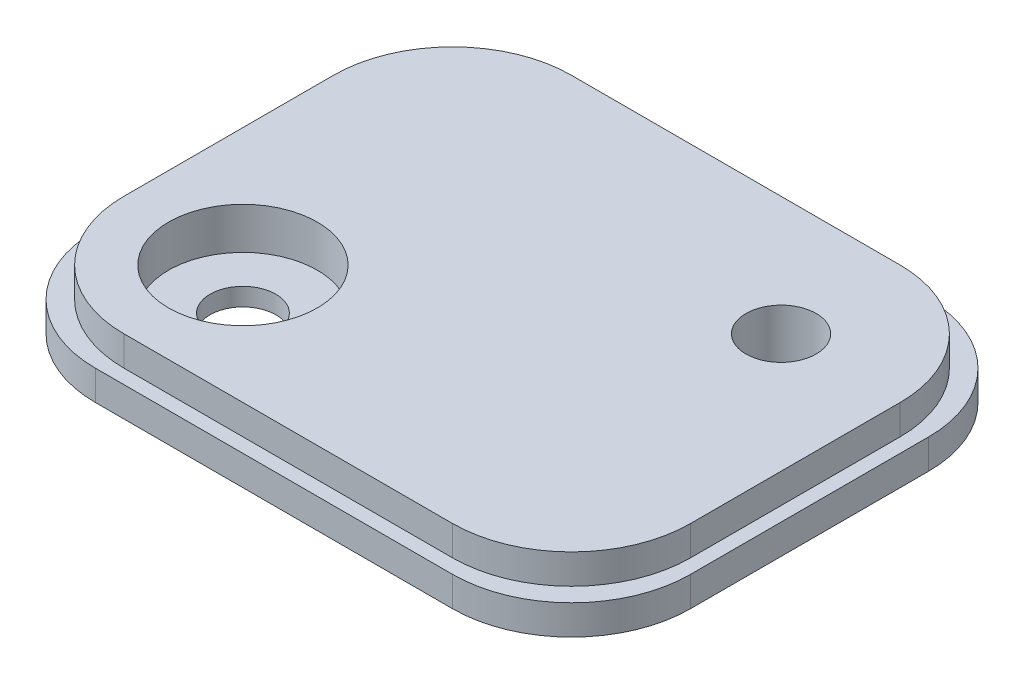
SolidWorks part; units mm, degrees
ref_plane "Front Plane" through (0, 0, 0) normal (0, 0, 1) x (1, 0, 0)
ref_plane "Top Plane" through (0, 0, 0) normal (0, 1, 0) x (1, 0, 0)
ref_plane "Right Plane" through (0, 0, 0) normal (1, 0, 0) x (0, 0, -1)
sketch "Sketch1" plane through (0, 0, 0) normal (0, 1, 0) x (1, 0, 0)
  line L1 (-30, 40) -> (30, 40)
  line L2 (-50, 20) -> (-50, -20)
  line L3 (-30, -40) -> (30, -40)
  line L4 (50, 20) -> (50, -20)
  line L5 (-50, 40) -> (50, -40) construction
  line L6 (-50, -40) -> (50, 40) construction
  arc A0 (30, -40) -> (50, -20) centre (30, -20) ccw
  arc A1 (-30, -40) -> (-50, -20) centre (-30, -20) cw
  arc A2 (30, 40) -> (50, 20) centre (30, 20) cw
  arc A3 (-30, 40) -> (-50, 20) centre (-30, 20) ccw
  point P0 (0, 0)
  dimension "D3" = 20
  dimension "D1" = 100
  dimension "D2" = 80
extrude "Boss-Extrude1" add sketch "Sketch1" along normal blind 5
ref_plane "Plane1" through (0, 5, 0) normal (0, 1, 0) x (1, 0, 0)
sketch "Sketch2" plane through (0, 5, 0) normal (0, 1, 0) x (1, 0, 0)
  line L1 (27.6, -37.6) -> (-27.6, -37.6)
  line L2 (47.6, -17.6) -> (47.6, 17.6)
  line L3 (27.6, 37.6) -> (-27.6, 37.6)
  line L4 (-47.6, -17.6) -> (-47.6, 17.6)
  line L5 (47.6, -37.6) -> (-47.6, 37.6) construction
  line L6 (47.6, 37.6) -> (-47.6, -37.6) construction
  arc A0 (-47.6, -17.6) -> (-27.6, -37.6) centre (-27.6, -17.6) ccw
  arc A1 (-27.6, 37.6) -> (-47.6, 17.6) centre (-27.6, 17.6) ccw
  arc A2 (27.6, 37.6) -> (47.6, 17.6) centre (27.6, 17.6) cw
  arc A3 (47.6, -17.6) -> (27.6, -37.6) centre (27.6, -17.6) cw
  point P0 (0, 0)
  dimension "D3" = 20
  dimension "D1" = 95.2
  dimension "D2" = 75.2
extrude "Boss-Extrude2" add sketch "Sketch2" along normal blind 5
ref_plane "Plane2" through (0, 10, 0) normal (0, 1, 0) x (1, 0, 0)
sketch "Sketch3" plane through (0, 10, 0) normal (0, 1, 0) x (1, 0, 0)
  line L0 (27.6, 37.6) -> (-27.6, 37.6) construction
  line L1 (47.6, -17.6) -> (47.6, 17.6) construction
  circle A0 centre (27.6, 17.6) radius 5.9
  dimension "D1" = 11.8
  dimension "D2" = 20
  dimension "D3" = 20
extrude "Cut-Extrude1" cut sketch "Sketch3" against normal blind 8.5
ref_plane "Plane3" through (0, 1.5, 0) normal (0, 1, 0) x (1, 0, 0)
sketch "Sketch4" plane through (0, 1.5, 0) normal (0, 1, 0) x (1, 0, 0)
  circle A0 centre (27.6, 17.6) radius 1.5
  dimension "D1" = 3
extrude "Cut-Extrude2" cut sketch "Sketch4" against normal blind 1.5
sketch "Sketch6" plane through (0, 10, 0) normal (0, 1, 0) x (1, 0, 0)
  line L0 (-47.6, 17.6) -> (-47.6, -17.6) construction
  line L1 (-27.6, -37.6) -> (27.6, -37.6) construction
  circle A0 centre (-27.6, -17.6) radius 5.52
  dimension "D1" = 11.04
  dimension "D2" = 20
  dimension "D3" = 20
extrude "Cut-Extrude3" cut sketch "Sketch6" against normal blind 10
sketch "Sketch7" plane through (0, 10, 0) normal (0, 1, 0) x (1, 0, 0)
  circle A0 centre (-27.6, -17.6) radius 12.5
  dimension "D1" = 25
extrude "Cut-Extrude4" cut sketch "Sketch7" against normal blind 7
sketch "Sketch8" plane through (0, 0, 0) normal (0, -1, 0) x (-1, 0, 0)
  text T0 "         Door\r\n  Security System\r\n         "
extrude "Boss-Extrude3" add sketch "Sketch8" along normal blind 1
